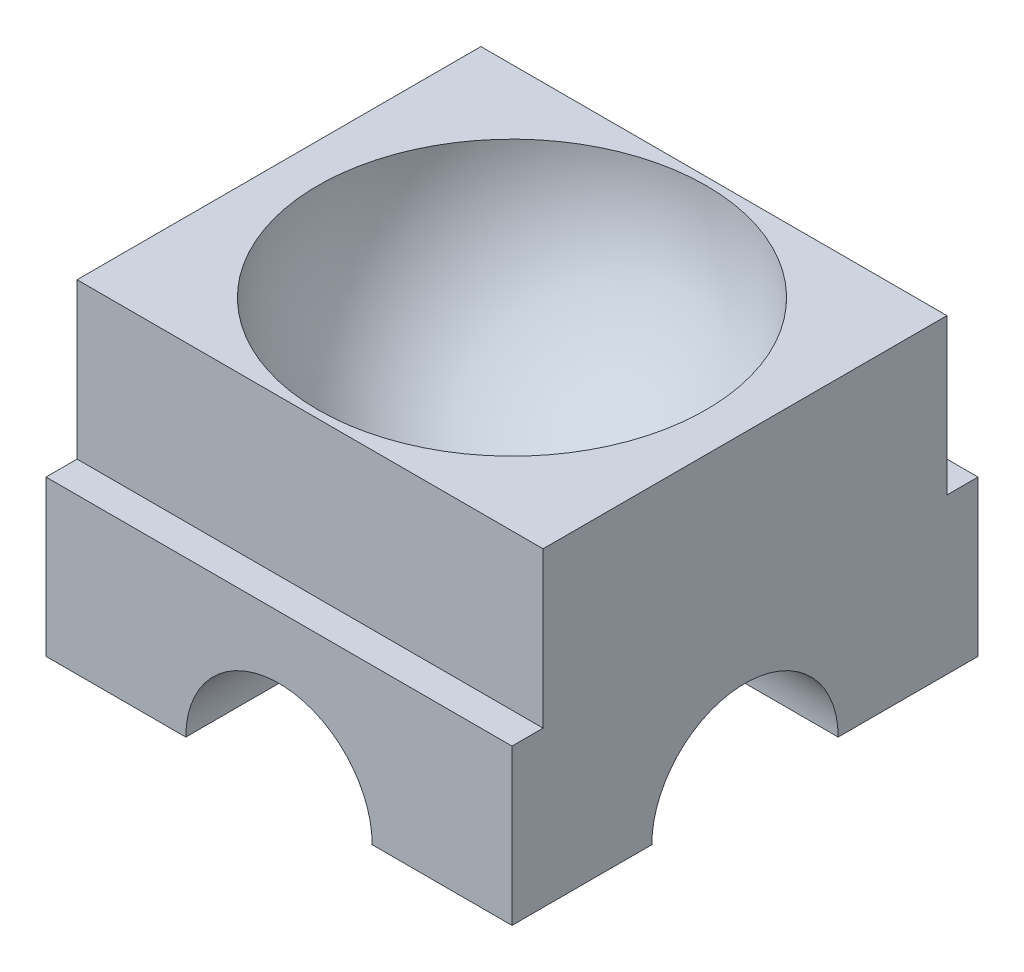
SolidWorks part; units mm, degrees
ref_plane "Front Plane" through (0, 0, 0) normal (0, 0, 1) x (1, 0, 0)
ref_plane "Top Plane" through (0, 0, 0) normal (0, 1, 0) x (1, 0, 0)
ref_plane "Right Plane" through (0, 0, 0) normal (1, 0, 0) x (0, 0, -1)
sketch "Sketch2" plane through (0, 0, 0) normal (0, 1, 0) x (1, 0, 0)
  line L1 (15, 15) -> (-15, 15)
  line L2 (15, 15) -> (15, -15)
  line L3 (15, -15) -> (-15, -15)
  line L4 (-15, 15) -> (-15, -15)
  line L5 (15, 15) -> (-15, -15) construction
  line L6 (15, -15) -> (-15, 15) construction
  point P0 (0, 0)
  dimension "D1" = 30
extrude "Boss-Extrude1" add sketch "Sketch2" along normal blind 20
sketch "Sketch3" plane through (0, 0, 15) normal (0, 0, 1) x (1, 0, 0)
  line L0 (-15, 0) -> (15, 0) construction
  circle A0 centre (0, 0) radius 6
  dimension "D1" = 12
sketch "Sketch4" plane through (15, 0, 0) normal (1, 0, 0) x (0, 0, -1)
  line L0 (-15, 0) -> (15, 0) construction
  circle A0 centre (0, 0) radius 6
  dimension "D1" = 12
extrude "Cut-Extrude2" cut sketch "Sketch3" against normal through all both and the other way through all contours A0
extrude "Cut-Extrude3" cut sketch "Sketch4" against normal through all both and the other way through all contours A0
sketch "Sketch5" plane through (0, 20, 0) normal (0, 1, 0) x (1, 0, 0)
  line L0 (0, 0) -> (22.3706, 0) construction
  line L1 (0, 0) -> (0, 21.4767) construction
  line L2 (12.5, 0) -> (-12.5, 0)
  arc A4 (12.5, 0) -> (-12.5, 0) centre (0, 0) ccw
  point P17 (0, 0)
  dimension "D1" = 25
revolve "Cut-Revolve1" cut sketch "Sketch5" angle 360 about L2
sketch "Sketch7" plane through (0, 20, 0) normal (0, 1, 0) x (1, 0, 0)
  circle A0 centre (0, 0) radius 3.75
  dimension "D1" = 7.5
extrude "Cut-Extrude4" cut sketch "Sketch7" against normal through all
sketch "Sketch8" plane through (0, 0, 15) normal (0, 0, 1) x (1, 0, 0)
  line L0 (15, 20) -> (15, 0) construction
  line L1 (15, 10) -> (-15, 10)
  line L2 (15, 10) -> (15, 20)
  line L3 (15, 20) -> (-15, 20)
  line L4 (-15, 10) -> (-15, 20)
extrude "Cut-Extrude6" cut sketch "Sketch8" against normal blind 2
sketch "Sketch9" plane through (0, 0, -15) normal (0, 0, -1) x (-1, 0, 0)
  line L0 (15, 20) -> (15, 0) construction
  line L1 (-15, 20) -> (15, 20)
  line L2 (-15, 20) -> (-15, 10)
  line L3 (-15, 10) -> (15, 10)
  line L4 (15, 20) -> (15, 10)
extrude "Cut-Extrude7" cut sketch "Sketch9" against normal blind 2
